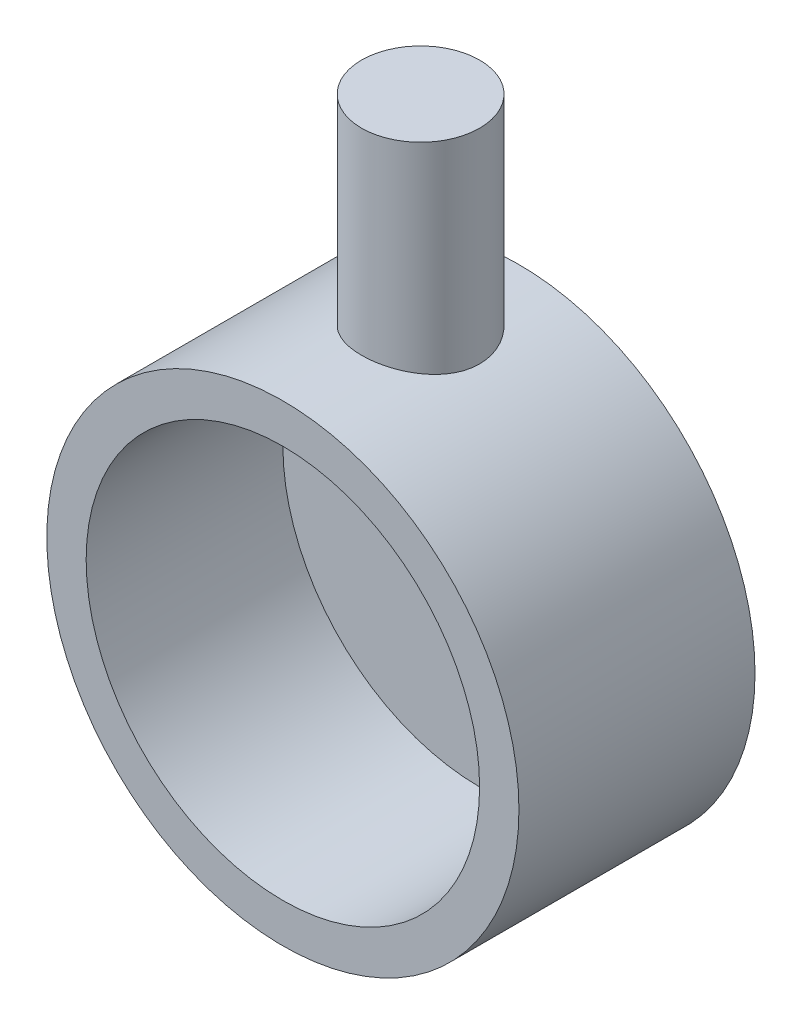
SolidWorks part; units mm, degrees
ref_plane "Front" through (0, 0, 0) normal (0, 0, 1) x (1, 0, 0)
ref_plane "Top" through (0, 0, 0) normal (0, 1, 0) x (1, 0, 0)
ref_plane "Right" through (0, 0, 0) normal (1, 0, 0) x (0, 0, -1)
sketch "草图1" plane through (0, 0, 0) normal (0, 0, 1) x (1, 0, 0)
  circle A0 centre (0, 0) radius 30
extrude "凸台-拉伸1" add sketch "草图1" along normal blind 30
sketch "草图2" plane through (0, 0, 30) normal (0, 0, 1) x (1, 0, 0)
  circle A0 centre (0, 0) radius 25
extrude "切除-拉伸1" [suppressed] cut sketch "草图2" against normal blind 25
sketch "草图3" plane through (0, 0, 0) normal (0, 1, 0) x (1, 0, 0)
  circle A0 centre (0, -12.5) radius 7.5
extrude "凸台-拉伸2" add sketch "草图3" along normal blind 55
sketch "草图4" plane through (0, 0, 30) normal (0, 0, 1) x (1, 0, 0)
  circle A0 centre (0, 0) radius 25
extrude "切除-拉伸2" cut sketch "草图4" against normal blind 25
